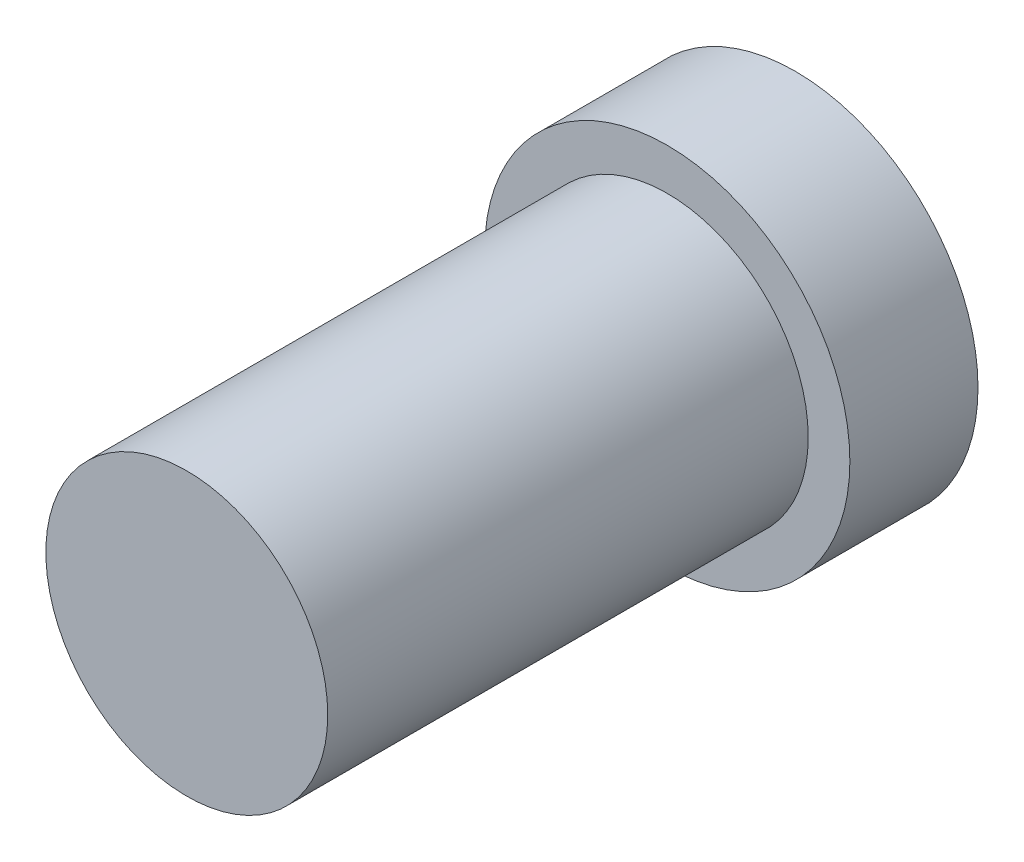
SolidWorks part; units mm, degrees
ref_plane "Front Plane" through (0, 0, 0) normal (0, 0, 1) x (1, 0, 0)
ref_plane "Top Plane" through (0, 0, 0) normal (0, 1, 0) x (1, 0, 0)
ref_plane "Right Plane" through (0, 0, 0) normal (1, 0, 0) x (0, 0, -1)
sketch "Sketch1" plane through (0, 0, 0) normal (0, 1, 0) x (1, 0, 0)
  line L0 (0, 0) -> (0, 92.9022) construction
  line L1 (0, 0) -> (-22, 0)
  line L2 (-22, 0) -> (-22, 75)
  line L3 (-22, 75) -> (-28.5, 75)
  line L4 (-28.5, 75) -> (-28.5, 95)
  line L5 (-28.5, 95) -> (0, 95)
  line L6 (0, 95) -> (0, 0)
  dimension "D1" = 44
  dimension "D2" = 75
  dimension "D3" = 57
  dimension "D4" = 20
revolve "Revolve1" add sketch "Sketch1" angle 360 about L0
